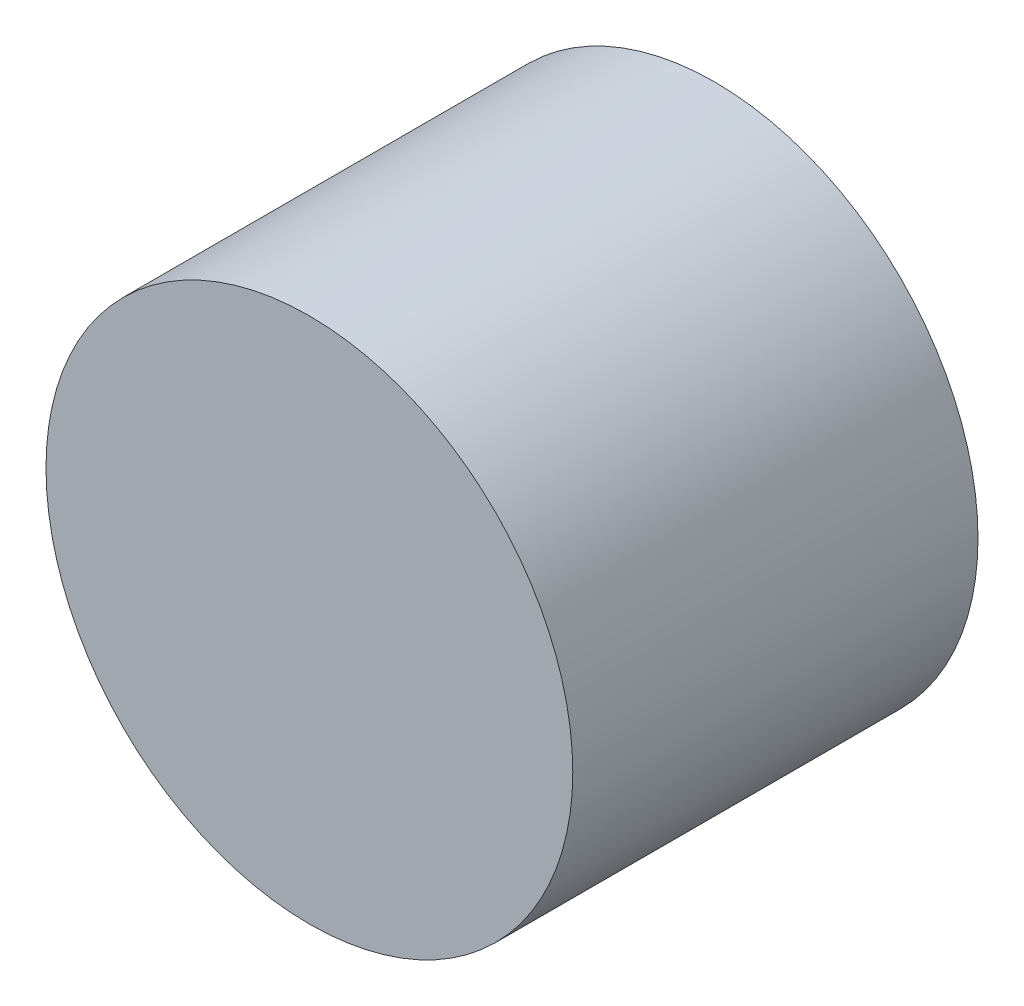
SolidWorks part; units mm, degrees
material "AISI 1020"
ref_plane "Спереди" through (0, 0, 0) normal (0, 0, 1) x (1, 0, 0)
ref_plane "Сверху" through (0, 0, 0) normal (0, 1, 0) x (1, 0, 0)
ref_plane "Справа" through (0, 0, 0) normal (1, 0, 0) x (0, 0, -1)
sketch "Эскиз1" plane through (0, 0, 0) normal (1, 0, 0) x (0, 0, -1)
  line L0 (-1000, 0) -> (49000, 0) construction
  line L1 (-6.3509, 0) -> (0, 11)
  line L2 (0, -12) -> (0, 12) construction
  line L3 (0, 11) -> (0, 13)
  line L4 (0, 13) -> (-20, 13)
  line L5 (-20, 13) -> (-20, 0)
  line L6 (-20, 0) -> (-6.3509, 0)
  line L7 (0, 13) -> (-297.0168, 13) construction
  dimension "D1" = 60
  dimension "D2" = 20
  dimension "D3" = 22
revolve "Повернуть1" add sketch "Эскиз1" angle 360 about L0
